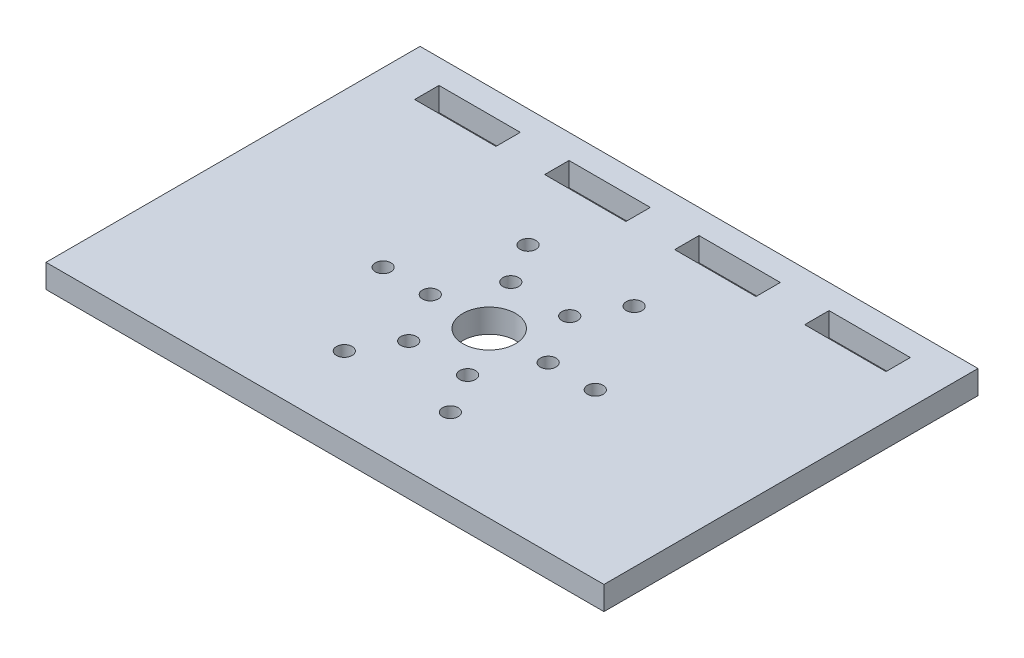
SolidWorks part; units mm, degrees
ref_plane "Front Plane" through (0, 0, 0) normal (0, 0, 1) x (1, 0, 0)
ref_plane "Top Plane" through (0, 0, 0) normal (0, 1, 0) x (1, 0, 0)
ref_plane "Right Plane" through (0, 0, 0) normal (1, 0, 0) x (0, 0, -1)
sketch "Sketch2" plane through (0, 0, 0) normal (0, 1, 0) x (1, 0, 0)
  line L0 (0, 0) -> (71, 0)
  line L1 (71, 0) -> (71, 47.6)
  line L2 (71, 47.6) -> (0, 47.6)
  line L3 (0, 47.6) -> (0, 0)
  line L9 (0, 44.5) -> (5.512, 44.5)
  line L11 (5.512, 44.5) -> (15.856, 44.5)
  line L12 (5.512, 44.5) -> (5.512, 41.4)
  line L13 (5.512, 41.4) -> (15.856, 41.4)
  line L14 (15.856, 41.4) -> (15.856, 44.5)
  line L16 (22.056, 44.5) -> (32.4, 44.5)
  line L17 (22.056, 44.5) -> (22.056, 41.4)
  line L18 (22.056, 41.4) -> (32.4, 41.4)
  line L19 (32.4, 41.4) -> (32.4, 44.5)
  line L20 (38.6, 44.5) -> (48.944, 44.5)
  line L21 (48.944, 44.5) -> (48.944, 41.4)
  line L22 (48.944, 41.4) -> (38.6, 41.4)
  line L23 (38.6, 41.4) -> (38.6, 44.5)
  line L24 (55.144, 44.5) -> (65.488, 44.5)
  line L25 (65.488, 44.5) -> (65.488, 41.4)
  line L26 (65.488, 41.4) -> (55.144, 41.4)
  line L27 (55.144, 41.4) -> (55.144, 44.5)
  circle A0 centre (35.5, 20.9) radius 3.35
  circle A1 centre (43, 20.9) radius 1
  circle A2 centre (49, 20.9) radius 1
  circle A3 centre (39.25, 14.4048) radius 1
  circle A4 centre (42.25, 9.2087) radius 1
  circle A5 centre (31.75, 14.4048) radius 1
  circle A6 centre (28.75, 9.2087) radius 1
  circle A7 centre (28, 20.9) radius 1
  circle A8 centre (22, 20.9) radius 1
  circle A9 centre (31.75, 27.3952) radius 1
  circle A10 centre (28.75, 32.5913) radius 1
  circle A11 centre (39.25, 27.3952) radius 1
  circle A12 centre (42.25, 32.5913) radius 1
  point P34 (35.5, 20.9)
  dimension "D3" = 20.9
  dimension "D4" = 2
  dimension "D5" = 2
  dimension "D6" = 6.7
  dimension "D7" = 7.5
  dimension "D8" = 6
  dimension "D1" = 71
  dimension "D2" = 47.6
  dimension "D10" = 5.512
  dimension "D11" = 3.1
  dimension "D12" = 10.344
  dimension "D13" = 3.1
  dimension "D14" = 10.344
  dimension "D15" = 6.2
  dimension "D16" = 6.2
  dimension "D17" = 10.344
  dimension "D18" = 10.344
  dimension "D19" = 6.2
  dimension "D20" = 5.512
  dimension "D9" = 6
extrude "Boss-Extrude1" add sketch "Sketch2" along normal blind 3
